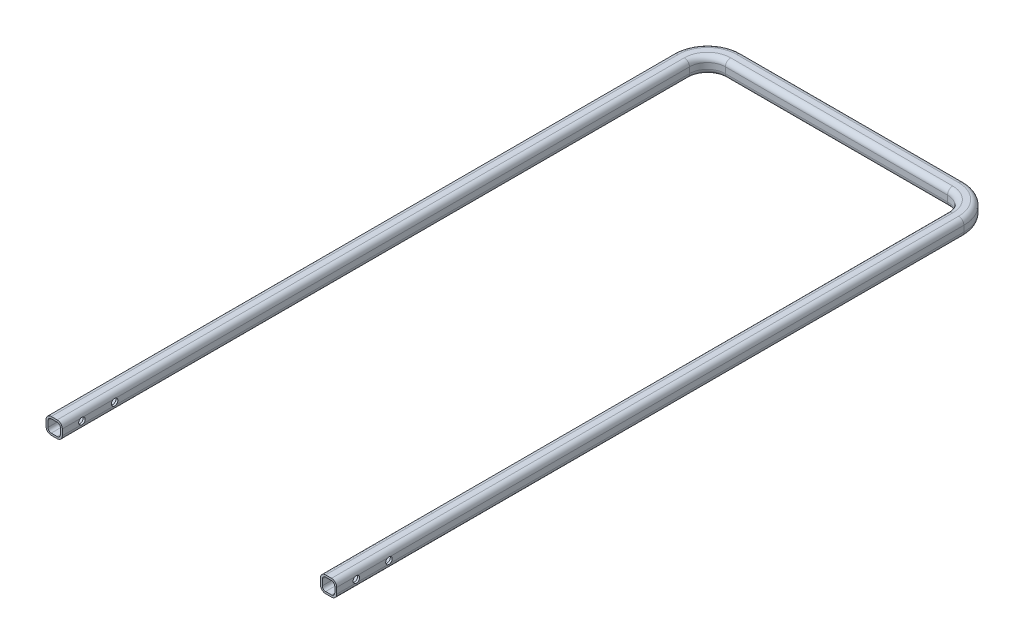
SolidWorks part; units mm, degrees
ref_plane "Front Plane" through (0, 0, 0) normal (0, 0, 1) x (1, 0, 0)
ref_plane "Top Plane" through (0, 0, 0) normal (0, 1, 0) x (1, 0, 0)
ref_plane "Right Plane" through (0, 0, 0) normal (1, 0, 0) x (0, 0, -1)
sketch "Sketch1" plane through (0, 0, 0) normal (0, 1, 0) x (1, 0, 0)
  line L0 (0, 0) -> (0, 960)
  line L1 (40, 1000) -> (380, 1000)
  line L2 (420, 960) -> (420, 0)
  line L3 (0, 660) -> (420, 660) construction
  line L4 (0, 360) -> (420, 360) construction
  line L5 (420, 360) -> (420, 660) construction
  arc A0 (380, 1000) -> (420, 960) centre (380, 960) cw
  arc A1 (40, 1000) -> (0, 960) centre (40, 960) ccw
  point P7 (420, 1000)
  point P10 (0, 1000)
  dimension "D3" = 40
  dimension "D4" = 300
  dimension "D1" = 1000
  dimension "D2" = 420
  dimension "D5" = 300
ref_plane "Plane1" through (0, 0, 0) normal (0, 0, 1) x (1, 0, 0)
sketch "Sketch3" plane through (0, 0, 0) normal (0, 0, 1) x (1, 0, 0)
  line L1 (-4.5, -9.5) -> (4.5, -9.5)
  line L2 (-9.5, -4.5) -> (-9.5, 4.5)
  line L3 (-4.5, 9.5) -> (4.5, 9.5)
  line L4 (9.5, -4.5) -> (9.5, 4.5)
  line L5 (-9.5, -9.5) -> (9.5, 9.5) construction
  line L6 (-9.5, 9.5) -> (9.5, -9.5) construction
  arc A0 (-4.5, 9.5) -> (-9.5, 4.5) centre (-4.5, 4.5) ccw
  arc A1 (-9.5, -4.5) -> (-4.5, -9.5) centre (-4.5, -4.5) ccw
  arc A2 (4.5, -9.5) -> (9.5, -4.5) centre (4.5, -4.5) ccw
  arc A3 (9.5, 4.5) -> (4.5, 9.5) centre (4.5, 4.5) ccw
  point P0 (0, 0)
  dimension "D3" = 5
  dimension "D1" = 19
  dimension "D2" = 19
sweep "Sweep-Thin1" add profiles "Sketch3" path "Sketch1" parameters "D1"=3
sketch "Sketch4" plane through (0, 0, 0) normal (1, 0, 0) x (0, 0, -1)
  line L0 (0, 0) -> (960, 0) construction
  circle A0 centre (30, 0) radius 5
  circle A1 centre (80, 0) radius 5
  dimension "D1" = 30
  dimension "D2" = 80
extrude "Cut-Extrude2" cut sketch "Sketch4" against normal through all both and the other way through all
ref_plane "Plane4" through (420, 0, 0) normal (-1, 0, 0) x (0, 0, 1)
sketch "Sketch8" plane through (420, 0, 0) normal (-1, 0, 0) x (0, 0, 1)
  line L0 (-660, 0) -> (-360, 0) construction
  line L1 (-510, 0) -> (-510, -61.9086) construction
ref_plane "Plane5" through (0, 0, 0) normal (1, 0, 0) x (0, 0, -1)
